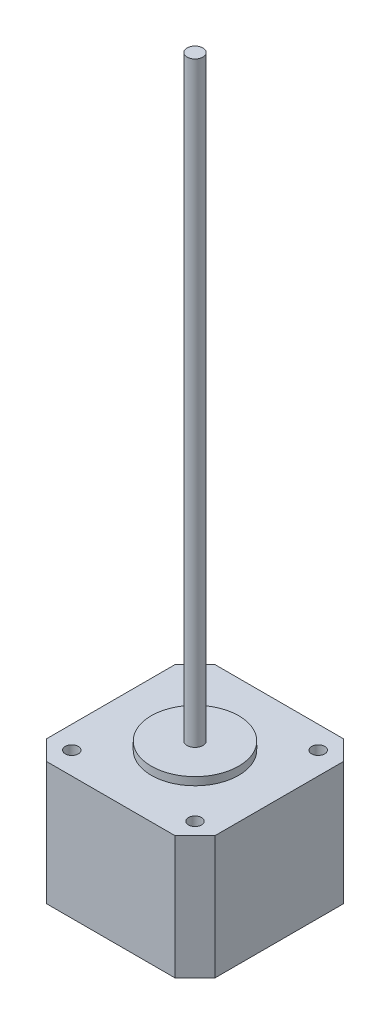
SolidWorks part; units mm, degrees
ref_plane "Front Plane" through (0, 0, 0) normal (0, 0, 1) x (1, 0, 0)
ref_plane "Top Plane" through (0, 0, 0) normal (0, 1, 0) x (1, 0, 0)
ref_plane "Right Plane" through (0, 0, 0) normal (1, 0, 0) x (0, 0, -1)
sketch "Sketch1" plane through (0, 0, 0) normal (0, 1, 0) x (1, 0, 0)
  line L1 (0, 0) -> (42.3, 0)
  line L2 (0, 0) -> (0, 42.3)
  line L3 (0, 42.3) -> (42.3, 42.3)
  line L4 (42.3, 0) -> (42.3, 42.3)
  dimension "D1" = 42.3
  dimension "D2" = 42.3
extrude "Boss-Extrude1" add sketch "Sketch1" along normal blind 31
sketch "Sketch2" plane through (0, 31, 0) normal (0, 1, 0) x (-1, 0, 0)
  line L0 (-42.3, -42.3) -> (0, -42.3) construction
  line L2 (0, -42.3) -> (0, 0) construction
  circle A0 centre (-5.65, -36.65) radius 1.6445
  circle A1 centre (-36.65, -36.65) radius 1.6445
  circle A2 centre (-5.65, -5.65) radius 1.6445
  circle A3 centre (-36.65, -5.65) radius 1.6445
  point P2 (-21.15, -42.3)
  point P9 (0, -21.15)
  dimension "D1" = 15.5
  dimension "D2" = 15.5
  dimension "D3" = 2
  dimension "D4" = 2
extrude "Cut-Extrude1" cut sketch "Sketch2" against normal blind 10
sketch "Sketch3" plane through (0, 31, 0) normal (0, 1, 0) x (-1, 0, 0)
  circle A0 centre (-21.15, -21.15) radius 11
  dimension "D1" = 22
extrude "Boss-Extrude2" add sketch "Sketch3" along normal blind 2
chamfer "Chamfer2" distance 5 angle 45 4 edges at (42.3, 15.5, 0) (0, 15.5, 0) (0, 15.5, -42.3) (42.3, 15.5, -42.3)
sketch "Sketch4" plane through (0, 33, 0) normal (0, 1, 0) x (-1, 0, 0)
  circle A0 centre (-21.15, -21.15) radius 2
  dimension "D1" = 4
extrude "Boss-Extrude3" add sketch "Sketch4" along normal blind 150
sketch "Sketch5" plane through (0, 0, 0) normal (0, -1, 0) x (1, 0, 0)
  circle A0 centre (21.15, -21.15) radius 2.5
  dimension "D1" = 5
extrude "Boss-Extrude4" add sketch "Sketch5" along normal blind 13.5
